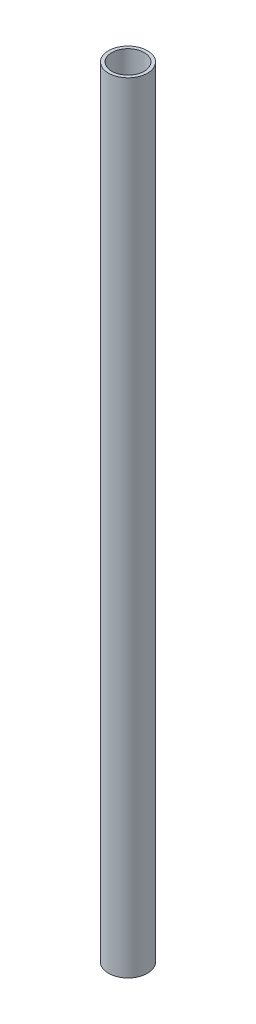
SolidWorks part; units mm, degrees
material "Acrylic (Medium-high impact)"
ref_plane "Front Plane" through (0, 0, 0) normal (0, 0, 1) x (1, 0, 0)
ref_plane "Top Plane" through (0, 0, 0) normal (0, 1, 0) x (1, 0, 0)
ref_plane "Right Plane" through (0, 0, 0) normal (1, 0, 0) x (0, 0, -1)
sketch "Sketch1" plane through (0, 0, 0) normal (0, 1, 0) x (1, 0, 0)
  circle A0 centre (0, 0) radius 30.48
  circle A1 centre (0, 0) radius 25.4
  dimension "D1" = 50.8
  dimension "D2" = 5.08
extrude "Boss-Extrude1" add sketch "Sketch1" along normal mid plane 1219.2
